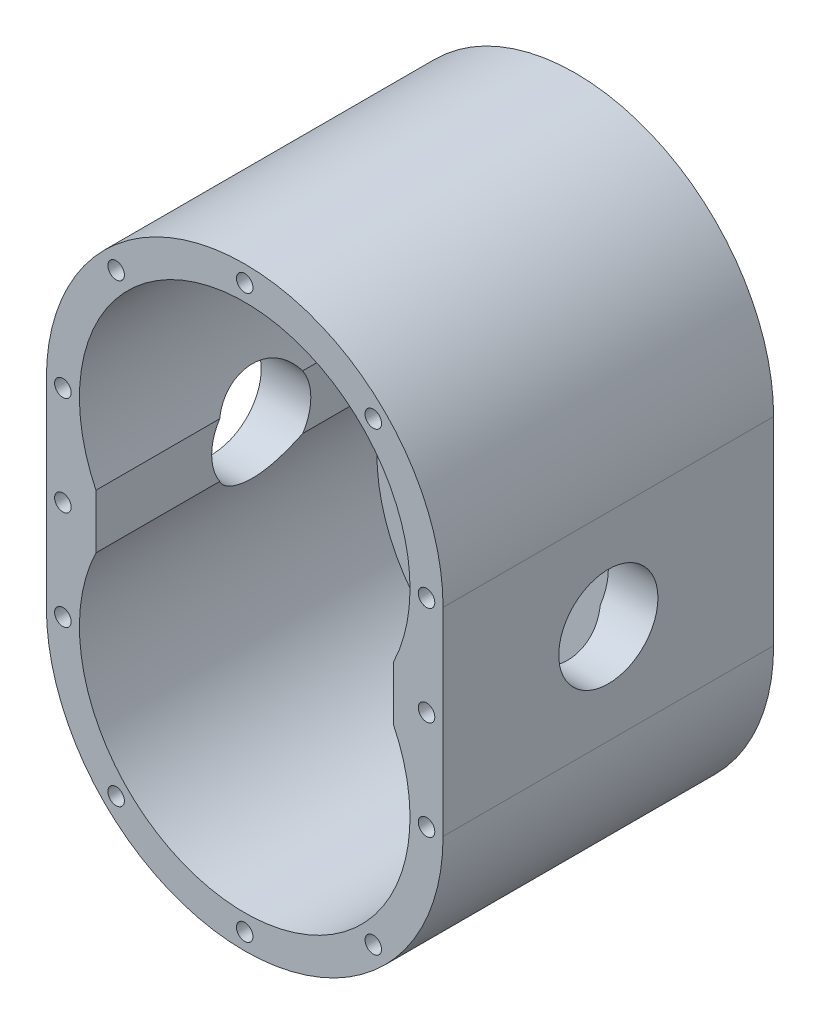
SolidWorks part; units mm, degrees
material "6061-T6 (SS)"
ref_plane "Front Plane" through (0, 0, 0) normal (0, 0, 1) x (1, 0, 0)
ref_plane "Top Plane" through (0, 0, 0) normal (0, 1, 0) x (1, 0, 0)
ref_plane "Right Plane" through (0, 0, 0) normal (1, 0, 0) x (0, 0, -1)
sketch "Sketch1" plane through (0, 0, 0) normal (0, 0, 1) x (1, 0, 0)
  line L0 (-60, 30) -> (-60, -30)
  line L1 (60, -30) -> (60, 30)
  arc A0 (-60, -30) -> (60, -30) centre (0, -30) ccw
  arc A1 (60, 30) -> (-60, 30) centre (0, 30) ccw
  point P8 (0, -90)
  point P10 (0, 90)
  point P11 (0, 0)
  point P12 (60, 0)
  point P13 (-60, 0)
  dimension "D2" = 60
  dimension "D1" = 60
extrude "Outer Housing Extrude" add sketch "Sketch1" along normal mid plane 100
sketch "Sketch2" plane through (0, 0, 50) normal (0, 0, 1) x (1, 0, 0)
  line L0 (-45, 8.2055) -> (-45, -8.2055)
  line L1 (45, 8.2055) -> (45, -8.2055)
  arc A0 (45, 8.2055) -> (-45, 8.2055) centre (0, 30) ccw
  arc A1 (-45, -8.2055) -> (45, -8.2055) centre (0, -30) ccw
  dimension "D1" = 100
  dimension "D2" = 30
  dimension "D3" = 30
  dimension "D4" = 45
  dimension "D5" = 45
extrude "Inner Housing Cut" cut sketch "Sketch2" against normal blind 90
sketch "Sketch3" plane through (0, 0, -40) normal (0, 0, 1) x (1, 0, 0)
  circle A0 centre (0, 30) radius 10
  circle A1 centre (0, -30) radius 10
  dimension "D2" = 30
  dimension "D3" = 20
  dimension "D4" = 20
  dimension "D1" = 30
extrude "Shaft Bearing Insert Hole" cut sketch "Sketch3" against normal blind 7
sketch "Sketch4" plane through (-60, 0, 0) normal (-1, 0, 0) x (0, 0, 1)
  circle A0 centre (0, 0) radius 15
  dimension "D1" = 30
extrude "High Pressure Outlet Hole" cut sketch "Sketch4" against normal up to next
sketch "Sketch5" plane through (60, 0, 0) normal (1, 0, 0) x (0, 0, -1)
  circle A0 centre (0, 0) radius 15
  dimension "D1" = 30
extrude "Low Pressure Inlet Hole" cut sketch "Sketch5" against normal up to next
hole_wizard "M6x1.0 Tapped Hole1" positions "Sketch6" profile "Sketch7" tap size "M6x1.0" standard "ANSI Metric"
sketch "Sketch6" plane through (0, 0, 50) normal (0, 0, 1) x (1, 0, 0)
  arc A0 (45, 8.2055) -> (-45, 8.2055) centre (0, 30) ccw construction
  point P0 (0, 85)
  point P6 (0, 80)
  dimension "D1" = 5
sketch "Sketch7" plane through (0, 85, 50) normal (1, 0, 0) x (0, -1, 0)
  line L0 (0, 0) -> (0, 18.5022)
  line L1 (0, 18.5022) -> (2.5, 17)
  line L2 (2.5, 17) -> (2.5, 0)
  line L5 (2.5, 0) -> (0, 0)
  line L10 (0, 18.5022) -> (-2.5, 17) construction
  line L11 (0, -6.35) -> (0, 107.95) construction
  dimension "Tap Drill Dia." = 5
  dimension "Tap Drill Depth" = 17
  dimension "Drill Angle" = 118
cosmetic thread "Hole Thread1" parameters "D1"=12, "D2"=6
pattern_circular "Housing Cover Top Fastener Holes" count 8 over 360 about axis through (0, 30, 0) along (0, 0, 1) skipping 3, 4, 5 of "M6x1.0 Tapped Hole1"
mirror "Housing Cover Bottom Fastener Holes" about plane through (0, 0, 0) normal (0, 1, 0) of "Housing Cover Top Fastener Holes", "M6x1.0 Tapped Hole1"
hole_wizard "M6x1.0 Tapped Hole2" positions "Sketch8" profile "Sketch9" tap size "M6x1.0" standard "ANSI Metric"
sketch "Sketch8" plane through (0, 0, 50) normal (0, 0, 1) x (1, 0, 0)
  line L0 (-60, 30) -> (-60, -30) construction
  line L1 (60, -30) -> (60, 30) construction
  point P0 (-55, 0)
  point P2 (55, 0)
  dimension "D1" = 5
  dimension "D2" = 5
sketch "Sketch9" plane through (-55, 0, 50) normal (1, 0, 0) x (0, -1, 0)
  line L0 (0, 0) -> (0, 18.5022)
  line L1 (0, 18.5022) -> (2.5, 17)
  line L2 (2.5, 17) -> (2.5, 0)
  line L5 (2.5, 0) -> (0, 0)
  line L10 (0, 18.5022) -> (-2.5, 17) construction
  line L11 (0, -6.35) -> (0, 107.95) construction
  dimension "Tap Drill Dia." = 5
  dimension "Tap Drill Depth" = 17
  dimension "Drill Angle" = 118
cosmetic thread "Hole Thread2" parameters "D1"=12, "D2"=6
cosmetic thread "Hole Thread3" parameters "D1"=12, "D2"=6
equation "\"D3@Sketch2\"=\"Inner Housing Diameter Offset\""
equation "\"D5@Sketch2\"=\"Inner Housing Bridge Offset\""
equation "\"D2@Sketch1\"=\"D1@Sketch1\""
equation "\"Outer Housing Diameter\"= 120mm"
equation "\"Inner Housing Diameter\" = 5 / 6 * \"Outer Housing Diameter\""
equation "\"D1@Sketch2\"=\"Inner Housing Diameter\""
equation "\"Inner Housing Diameter Offset\"= \"Outer Housing Diameter\" / 4"
equation "\"Inner Housing Bridge Offset\"= \"Inner Housing Diameter Offset\" * 1.5"
equation "\"Outer Housing Diameter Offset\"= \"Outer Housing Diameter\" / 2"
equation "\"D2@Sketch2\"=\"Inner Housing Diameter Offset\""
equation "\"D4@Sketch2\"=\"Inner Housing Bridge Offset\""
equation "\"Housing Wall Thickness\"= 10mm"
equation "\"D1@Inner Housing Cut\" = \"Outer Housing Extrusion Length\" - \"Housing Wall Thickness\""
equation "\"Outer Housing Extrusion Length\"= 100mm"
equation "\"D1@Outer Housing Extrude\" = \"Outer Housing Extrusion Length\""
equation "\"D1@Sketch3\"=\"Inner Housing Diameter Offset\""
equation "\"D2@Sketch3\"=\"Inner Housing Diameter Offset\""
equation "\"Driven Shaft Hole Diameter\"= 20mm"
equation "\"Drive Shaft Hole Diameter\"= 20mm"
equation "\"D3@Sketch3\"=\"Driven Shaft Hole Diameter\""
equation "\"D4@Sketch3\"=\"Drive Shaft Hole Diameter\""
equation "\"Shaft Bearing Thickness\"= 7mm"
equation "\"D1@Shaft Bearing Insert Hole\" = \"Shaft Bearing Thickness\""
equation "\"High Pressure Outlet Diameter\"= 30mm"
equation "\"Low Pressure Inlet Diameter\"= 30mm"
equation "\"D1@Sketch4\"=\"High Pressure Outlet Diameter\""
equation "\"D1@Sketch5\"=\"Low Pressure Inlet Diameter\""
equation "\"D2@Sketch8\"=\"D1@Sketch8\""
